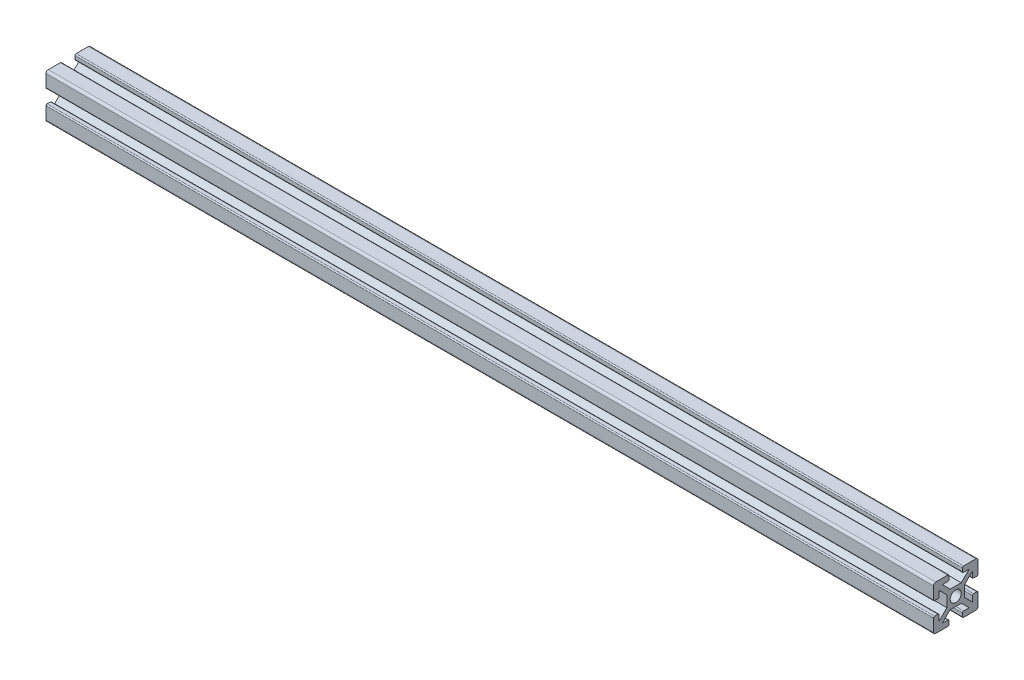
SolidWorks part; units mm, degrees
ref_plane "Front Plane" through (0, 0, 0) normal (0, 0, 1) x (1, 0, 0)
ref_plane "Top Plane" through (0, 0, 0) normal (0, 1, 0) x (1, 0, 0)
ref_plane "Right Plane" through (0, 0, 0) normal (1, 0, 0) x (0, 0, -1)
sketch "Sketch1" plane through (0, 0, 0) normal (0, 0, 1) x (1, 0, 0)
  line L0 (-188.3508, 0) -> (211.6492, 0)
  dimension "D1" = 400
other "Aluminium prof ALUMINIUM PROF(1)"
ref_plane "Plane1" through (-188.3508, 0, 0) normal (1, 0, 0) x (0, 1, 0)
sketch "Sketch11" plane through (-188.3508, 0, 0) normal (1, 0, 0) x (0, 1, 0)
  line L0 (0, 0) -> (0, 19.0058) construction
  line L9 (0, 0) -> (23.0409, 0) construction
  line L10 (23.0409, 0) -> (23.0409, -0.0585) construction
  line L11 (23.0409, -0.0585) -> (23.0409, 0) construction
  line L13 (-2.5, 4) -> (2.5, 4)
  line L14 (2.5, 4) -> (6.0355, 7.5355)
  line L15 (6.0355, 7.5355) -> (3.5355, 7.5355)
  line L16 (3.0355, 8.0355) -> (3.0355, 9.5355)
  line L17 (3.5355, 10.0355) -> (9.0355, 10.0355)
  line L18 (10.0355, 9.0355) -> (10.0355, 3.5355)
  line L19 (9.5355, 3.0355) -> (8.0355, 3.0355)
  line L20 (7.5355, 3.5355) -> (7.5355, 6.0355)
  line L21 (7.5355, 6.0355) -> (4, 2.5)
  line L22 (4, 2.5) -> (4, -2.5)
  line L23 (-10.0355, 9.0355) -> (-10.0355, 3.5355)
  line L24 (-4, 2.5) -> (-4, -2.5)
  line L25 (-7.5355, 6.0355) -> (-4, 2.5)
  line L26 (-7.5355, 3.5355) -> (-7.5355, 6.0355)
  line L27 (-9.5355, 3.0355) -> (-8.0355, 3.0355)
  line L28 (-3.5355, 10.0355) -> (-9.0355, 10.0355)
  line L29 (-3.0355, 8.0355) -> (-3.0355, 9.5355)
  line L30 (-6.0355, 7.5355) -> (-3.5355, 7.5355)
  line L31 (-2.5, 4) -> (-6.0355, 7.5355)
  line L32 (3.5355, -10.0355) -> (9.0355, -10.0355)
  line L33 (-2.5, -4) -> (-6.0355, -7.5355)
  line L34 (-6.0355, -7.5355) -> (-3.5355, -7.5355)
  line L35 (-3.0355, -8.0355) -> (-3.0355, -9.5355)
  line L36 (-3.5355, -10.0355) -> (-9.0355, -10.0355)
  line L37 (-9.5355, -3.0355) -> (-8.0355, -3.0355)
  line L38 (-7.5355, -3.5355) -> (-7.5355, -6.0355)
  line L39 (-7.5355, -6.0355) -> (-4, -2.5)
  line L40 (-10.0355, -9.0355) -> (-10.0355, -3.5355)
  line L41 (7.5355, -6.0355) -> (4, -2.5)
  line L42 (7.5355, -3.5355) -> (7.5355, -6.0355)
  line L43 (9.5355, -3.0355) -> (8.0355, -3.0355)
  line L44 (10.0355, -9.0355) -> (10.0355, -3.5355)
  line L45 (3.0355, -8.0355) -> (3.0355, -9.5355)
  line L46 (6.0355, -7.5355) -> (3.5355, -7.5355)
  line L47 (2.5, -4) -> (6.0355, -7.5355)
  line L48 (-2.5, -4) -> (2.5, -4)
  circle A0 centre (0, 0) radius 2.5
  arc A1 (-10.0355, 9.0355) -> (-9.0355, 10.0355) centre (-9.0355, 9.0355) cw
  arc A2 (-9.0355, -10.0355) -> (-10.0355, -9.0355) centre (-9.0355, -9.0355) cw
  arc A3 (9.0355, -10.0355) -> (10.0355, -9.0355) centre (9.0355, -9.0355) ccw
  arc A4 (9.0355, 10.0355) -> (10.0355, 9.0355) centre (9.0355, 9.0355) cw
  arc A5 (-9.5355, -3.0355) -> (-10.0355, -3.5355) centre (-9.5355, -3.5355) ccw
  arc A6 (-8.0355, -3.0355) -> (-7.5355, -3.5355) centre (-8.0355, -3.5355) cw
  arc A7 (-3.5355, -7.5355) -> (-3.0355, -8.0355) centre (-3.5355, -8.0355) cw
  arc A8 (-3.0355, -9.5355) -> (-3.5355, -10.0355) centre (-3.5355, -9.5355) cw
  arc A9 (3.5355, -10.0355) -> (3.0355, -9.5355) centre (3.5355, -9.5355) cw
  arc A10 (3.0355, -8.0355) -> (3.5355, -7.5355) centre (3.5355, -8.0355) cw
  arc A11 (9.5355, -3.0355) -> (10.0355, -3.5355) centre (9.5355, -3.5355) cw
  arc A12 (7.5355, -3.5355) -> (8.0355, -3.0355) centre (8.0355, -3.5355) cw
  arc A13 (10.0355, 3.5355) -> (9.5355, 3.0355) centre (9.5355, 3.5355) cw
  arc A14 (8.0355, 3.0355) -> (7.5355, 3.5355) centre (8.0355, 3.5355) cw
  arc A15 (3.5355, 7.5355) -> (3.0355, 8.0355) centre (3.5355, 8.0355) cw
  arc A16 (3.0355, 9.5355) -> (3.5355, 10.0355) centre (3.5355, 9.5355) cw
  arc A17 (-3.5355, 10.0355) -> (-3.0355, 9.5355) centre (-3.5355, 9.5355) cw
  arc A18 (-3.0355, 8.0355) -> (-3.5355, 7.5355) centre (-3.5355, 8.0355) cw
  arc A19 (-7.5355, 3.5355) -> (-8.0355, 3.0355) centre (-8.0355, 3.5355) cw
  arc A20 (-10.0355, 3.5355) -> (-9.5355, 3.0355) centre (-9.5355, 3.5355) ccw
  point P26 (0, 4)
  point P29 (-4, 0)
  point P30 (4, 0)
  point P44 (0, -4)
  point P48 (-10.0355, 10.0355)
  point P51 (-10.0355, -10.0355)
  point P54 (10.0355, -10.0355)
  point P57 (10.0355, 10.0355)
  point P60 (-10.0355, -3.0355)
  point P63 (-7.5355, -3.0355)
  point P66 (-3.0355, -7.5355)
  point P69 (-3.0355, -10.0355)
  point P72 (3.0355, -10.0355)
  point P75 (3.0355, -7.5355)
  point P78 (10.0355, -3.0355)
  point P81 (7.5355, -3.0355)
  point P84 (10.0355, 3.0355)
  point P87 (7.5355, 3.0355)
  point P90 (3.0355, 7.5355)
  point P93 (3.0355, 10.0355)
  point P96 (-3.0355, 10.0355)
  point P99 (-3.0355, 7.5355)
  point P102 (-7.5355, 3.0355)
  point P105 (-10.0355, 3.0355)
  point P106 (0, 0)
  dimension "D5" = 4
  dimension "D12" = 1
  dimension "D13" = 0.5
  dimension "D1" = 135
  dimension "D2" = 2.5
  dimension "D3" = 4
  dimension "D4" = 2.5
  dimension "D6" = 7
  dimension "D7" = 7
  dimension "D8" = 3
  dimension "D9" = 3
  dimension "D10" = 5
  dimension "D11" = 23.0409
sketch "Sketch12" plane through (0, 0, -4) normal (0, 0, -1) x (-1, 0, 0)
  line L0 (-211.6492, 0) -> (-192.3967, 0) construction
  line L1 (-211.6492, -2.5) -> (-211.6492, 2.5) construction
  circle A0 centre (-201.6492, 0) radius 2.5
  dimension "D2" = 5
  dimension "D1" = 10
extrude "Cut-Extrude1" cut sketch "Sketch12" against normal blind 10
